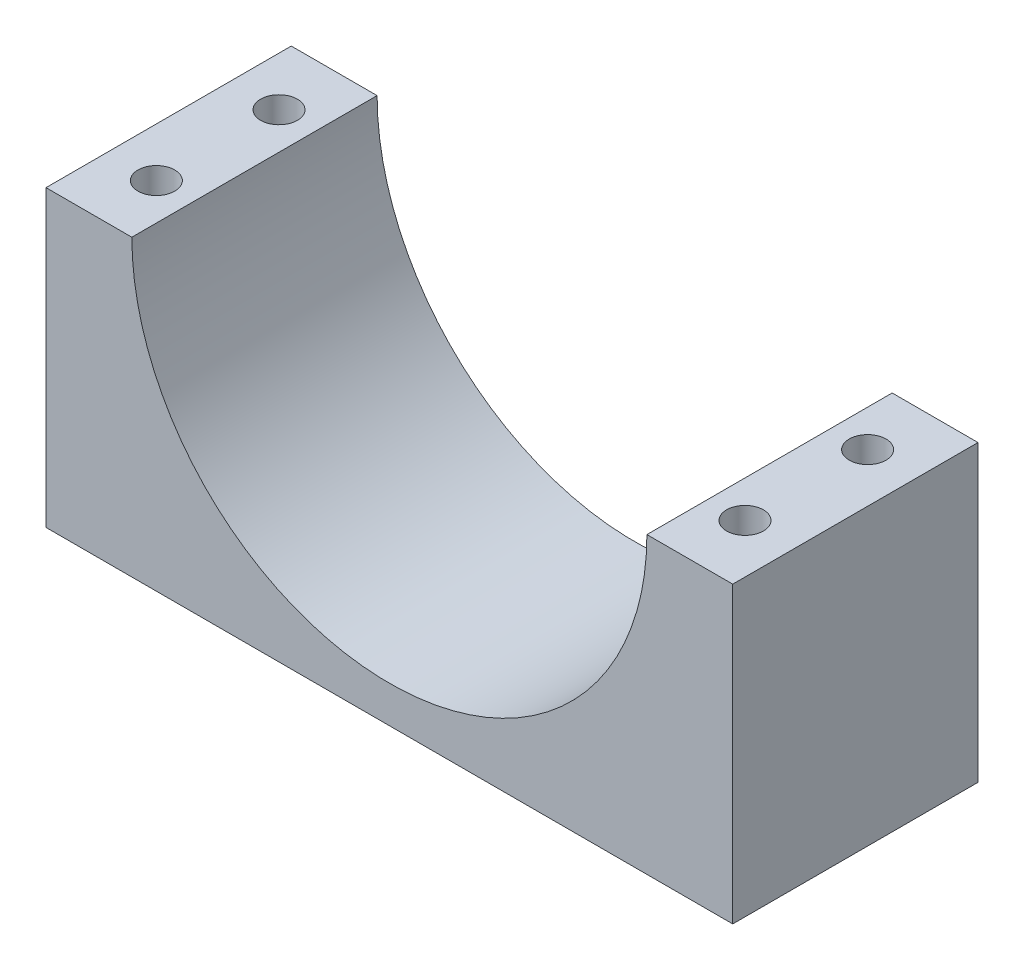
SolidWorks part; units mm, degrees
ref_plane "前视基准面" through (0, 0, 0) normal (0, 0, 1) x (1, 0, 0)
ref_plane "上视基准面" through (0, 0, 0) normal (0, 1, 0) x (1, 0, 0)
ref_plane "右视基准面" through (0, 0, 0) normal (1, 0, 0) x (0, 0, -1)
sketch "草图1" plane through (0, 0, 0) normal (0, 0, 1) x (1, 0, 0)
  line L0 (-28, -24) -> (28, -24)
  line L2 (28, -24) -> (28, 0)
  line L3 (28, 0) -> (21, 0)
  line L4 (-28, -24) -> (-28, 0)
  line L5 (4, -24) -> (-28, 0) construction
  line L6 (28, 0) -> (-4, -24) construction
  line L7 (-21, 0) -> (-28, 0)
  arc A0 (-21, 0) -> (21, 0) centre (0, 0) ccw
  point P3 (0, -21)
  dimension "D1" = 42
  dimension "D2" = 28
  dimension "D3" = 28
  dimension "D4" = 0
  dimension "D5" = 3
extrude "凸台-拉伸1" add sketch "草图1" along normal blind 20
sketch "草图2" plane through (0, 0, 0) normal (0, 1, 0) x (1, 0, 0)
  line L0 (-21, -20) -> (-28, -20) construction
  line L1 (-21, 0) -> (-28, 0) construction
  line L2 (-28, -20) -> (-28, 0) construction
  circle A0 centre (-24, -5) radius 1.5
  circle A1 centre (-24, -15) radius 1.5
  dimension "D1" = 3
  dimension "D2" = 3
  dimension "D3" = 5
  dimension "D4" = 5
  dimension "D5" = 4
  dimension "D6" = 4
extrude "切除-拉伸1" cut sketch "草图2" against normal through all
mirror "镜向1" about plane through (0, 0, 0) normal (1, 0, 0) of "切除-拉伸1"
